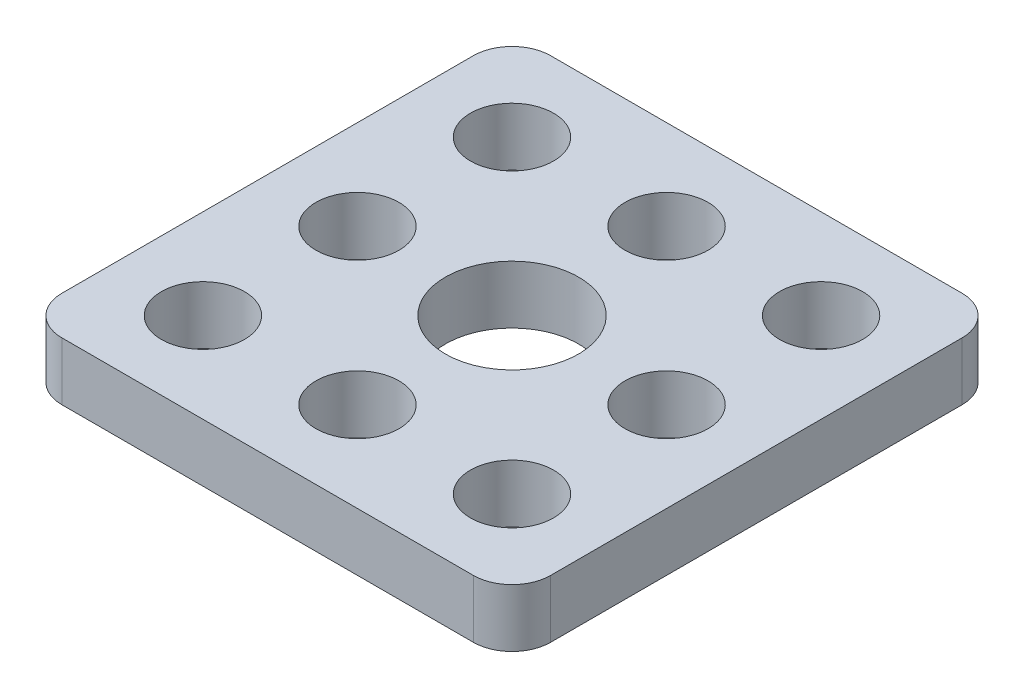
SolidWorks part; units mm, degrees
ref_plane "Front Plane" through (0, 0, 0) normal (0, 0, 1) x (1, 0, 0)
ref_plane "Top Plane" through (0, 0, 0) normal (0, 1, 0) x (1, 0, 0)
ref_plane "Right Plane" through (0, 0, 0) normal (1, 0, 0) x (0, 0, -1)
sketch "Sketch1" plane through (0, 0, 0) normal (0, 1, 0) x (1, 0, 0)
  line L0 (4.65, 20.65) -> (20.65, 20.65) construction
  line L1 (0, 0) -> (25.3, 0)
  line L2 (0, 0) -> (0, 25.3)
  line L3 (0, 25.3) -> (25.3, 25.3)
  line L4 (25.3, 0) -> (25.3, 25.3)
  line L5 (20.65, 20.65) -> (20.65, 4.65) construction
  line L6 (20.65, 4.65) -> (4.65, 4.65) construction
  line L7 (4.65, 4.65) -> (4.65, 20.65) construction
  circle A0 centre (4.65, 4.65) radius 2.15
  circle A1 centre (12.65, 4.65) radius 2.15
  circle A2 centre (20.65, 4.65) radius 2.15
  circle A3 centre (4.65, 12.65) radius 2.15
  circle A4 centre (4.65, 20.65) radius 2.15
  circle A5 centre (20.65, 12.65) radius 2.15
  circle A6 centre (20.65, 20.65) radius 2.15
  circle A7 centre (12.65, 20.65) radius 2.15
  circle A8 centre (12.65, 12.65) radius 3.45
  point P22 (0, 12.65)
  point P24 (12.65, 0)
  dimension "D2" = 4.3
  dimension "D8" = 6.9
  dimension "D1" = 16
  dimension "D3" = 16
  dimension "D4" = 2.5
  dimension "D5" = 2.5
  dimension "D6" = 2.5
  dimension "D7" = 2.5
extrude "Boss-Extrude1" add sketch "Sketch1" along normal blind 3
fillet "Fillet1" radius 2 4 edges at (25.3, 1.5, 0) (0, 1.5, 0) (0, 1.5, -25.3) (25.3, 1.5, -25.3)
equation "\"width\"= 24"
equation "\"thk\"= 3"
equation "\"holesize\"= 4.2"
equation "\"holedistance\"= ( 20 + 12 ) / 2"
equation "\"threaded_hole\"= 3.9"
equation "\"fillet_radius\"= 2"
equation "\"ground_clearance\"= 25"
equation "\"tire_thk\"= 3"
equation "\"innerwheel_diam\" = \"wheel_diam\"-2*\"tire_thk\""
equation "\"innerwheel_thk\"= 8"
equation "\"wheel_diam\"= 2*(\"width\"/2+\"ground_clearance\")"
equation "\"D1@Boss-Extrude1\"=\"thk\""
equation "\"xnum\"= 3'Number of holes in x"
equation "\"ynum\"= 3'Number of holes in y"
equation "\"D1@Sketch1\"=\"holedistance\""
equation "\"D2@Sketch1\"=\"holesize\"+0.1"
equation "\"D3@Sketch1\"=\"holedistance\""
equation "\"D5@Sketch1\"=\"D4@Sketch1\""
equation "\"D6@Sketch1\"=\"D4@Sketch1\""
equation "\"D7@Sketch1\"=\"D4@Sketch1\""
equation "\"D1@Fillet1\"=\"fillet_radius\""
equation "\"coloursensor_holesize\"= 2.65"
equation "\"hole_to_edge\" = 4"
